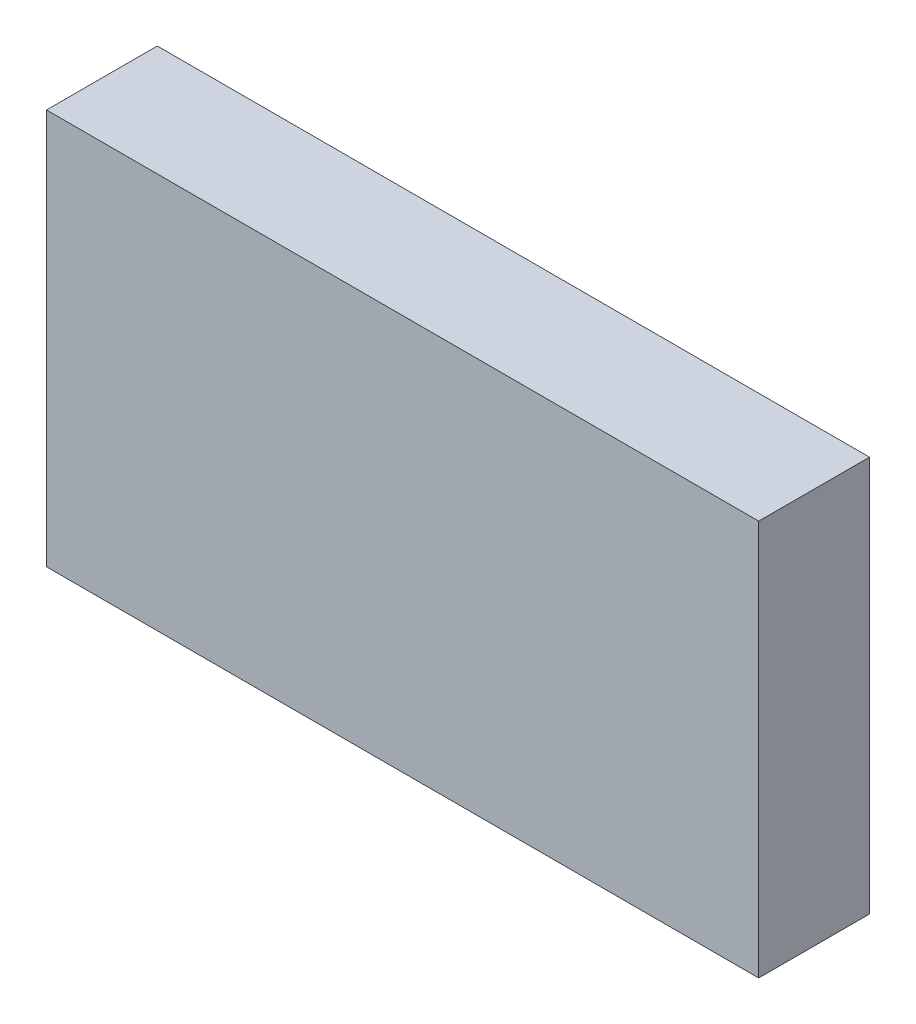
SolidWorks part; units mm, degrees
material "Pine"
ref_plane "Front Plane" through (0, 0, 0) normal (0, 0, 1) x (1, 0, 0)
ref_plane "Top Plane" through (0, 0, 0) normal (0, 1, 0) x (1, 0, 0)
ref_plane "Right Plane" through (0, 0, 0) normal (1, 0, 0) x (0, 0, -1)
sketch "Sketch1" plane through (0, 0, 0) normal (0, 0, 1) x (1, 0, 0)
  line L0 (8932.6508, -5243.5125) -> (10226.1458, -5243.5125)
  line L1 (9086.3208, -4722.0918) -> (10222.9708, -4853.7812)
  line L2 (8914.8708, -6342.0625) -> (10197.5708, -6342.0625)
  line L3 (8914.8708, -5808.6625) -> (10197.5708, -5808.6625)
  line L4 (8919.6333, -5253.0375) -> (10218.2083, -5253.0375)
  line L5 (9134.2633, -4656.1375) -> (9134.2633, -4638.3575)
  line L6 (9091.0833, -4638.3575) -> (9134.2633, -4638.3575)
  line L7 (9091.0833, -4567.2375) -> (9091.0833, -4638.3575)
  line L8 (9134.2633, -4656.1375) -> (9581.3033, -4656.1375)
  line L9 (9091.0833, -4567.2375) -> (9624.4833, -4567.2375)
  line L10 (9581.3033, -4656.1375) -> (9581.3033, -4638.3575)
  line L11 (9581.3033, -4638.3575) -> (9624.4833, -4638.3575)
  line L12 (9624.4833, -4567.2375) -> (9624.4833, -4638.3575)
  line L13 (8932.6508, -5225.7325) -> (9344.9775, -5225.7325)
  line L14 (8932.6508, -5256.2125) -> (8932.6508, -5243.5125)
  line L15 (8911.6958, -5256.2125) -> (8932.6508, -5256.2125)
  line L16 (8914.8708, -4722.0918) -> (9086.3208, -4722.0918)
  line L17 (8911.6958, -4715.5913) -> (8932.6508, -4715.5913)
  line L18 (8914.8708, -6342.0625) -> (8914.8708, -5808.6625)
  line L19 (12082.9917, -4722.0918) -> (10946.3417, -4853.7812)
  line L20 (12236.6617, -5243.5125) -> (10943.1667, -5243.5125)
  line L21 (10951.1042, -5253.0375) -> (12249.6792, -5253.0375)
  line L22 (10838.3917, -5656.2625) -> (11308.2917, -5656.2625)
  line L23 (10838.3917, -5719.7625) -> (11308.2917, -5719.7625)
  line L24 (10838.3917, -5742.5368) -> (11308.2917, -5742.5368)
  line L25 (10806.6417, -6342.0625) -> (11340.0417, -6342.0625)
  line L26 (10803.4667, -6335.7125) -> (11343.2167, -6335.7125)
  line L27 (10803.4667, -6317.9325) -> (11343.2167, -6317.9325)
  line L28 (10943.1667, -5225.7325) -> (11376.4483, -5225.7325)
  line L29 (11506.7292, -4754.5625) -> (10806.6417, -4827.5875)
  line L30 (11506.7292, -4567.2375) -> (11506.7292, -4754.5625)
  line L31 (10806.6417, -4567.2375) -> (10806.6417, -4827.5875)
  line L32 (10806.6417, -4567.2375) -> (11506.7292, -4567.2375)
  line L33 (10235.6708, -6329.3625) -> (10245.1958, -6329.3625)
  line L34 (10245.1958, -6329.3625) -> (10254.7208, -6278.5625)
  line L35 (10302.3458, -6329.3625) -> (10311.8708, -6278.5625)
  line L36 (10302.3458, -6329.3625) -> (10292.8208, -6329.3625)
  line L37 (10245.1958, -5821.3625) -> (10254.7208, -5872.1625)
  line L38 (10235.6708, -5821.3625) -> (10245.1958, -5821.3625)
  line L39 (10292.8208, -5821.3625) -> (10302.3458, -5821.3625)
  line L40 (10302.3458, -5821.3625) -> (10311.8708, -5872.1625)
  line L41 (10235.6708, -5821.3625) -> (10235.6708, -6329.3625)
  line L42 (10254.7208, -5872.1625) -> (10254.7208, -6278.5625)
  line L43 (10311.8708, -5872.1625) -> (10311.8708, -6278.5625)
  line L44 (10292.8208, -5821.3625) -> (10292.8208, -6329.3625)
  line L45 (8932.6508, -5225.7325) -> (8932.6508, -4715.5913)
  line L46 (8911.6958, -4715.5913) -> (8911.6958, -5256.2125)
  line L47 (8914.8708, -5248.275) -> (8914.8708, -4722.0918)
  line L48 (8919.6333, -5253.0375) -> (8914.8708, -5248.275)
  line L49 (8914.8708, -5145.0875) -> (8937.426, -5145.0875)
  line L50 (8914.8708, -5202.2375) -> (8937.426, -5202.2375)
  line L51 (10838.3917, -5656.2625) -> (10838.3917, -5719.7625)
  line L52 (10832.0417, -5736.1868) -> (10856.1717, -5736.1868)
  line L53 (10806.6417, -6342.0625) -> (10806.6417, -5818.7368)
  line L54 (10832.0417, -5649.9125) -> (10856.1717, -5649.9125)
  line L55 (10832.0417, -5726.1125) -> (10856.1717, -5726.1125)
  line L56 (10806.6417, -5818.7368) -> (10833.9015, -5818.7368)
  line L57 (10832.0417, -5806.0442) -> (10851.6815, -5806.0442)
  line L58 (10856.1717, -5801.5541) -> (10856.1717, -5736.1868)
  line L59 (10838.3917, -5814.2467) -> (10838.3917, -5742.5368)
  line L60 (10832.0417, -5806.0442) -> (10832.0417, -5736.1868)
  line L61 (10803.4667, -6317.9325) -> (10803.4667, -6335.7125)
  line L62 (10197.5708, -5808.6625) -> (10197.5708, -6342.0625)
  line L63 (9762.3842, -6348.4125) -> (9762.3842, -5802.3125)
  line L64 (9780.1642, -6348.4125) -> (9762.3842, -6348.4125)
  line L65 (9780.1642, -5802.3125) -> (9780.1642, -6348.4125)
  line L66 (9762.3842, -5802.3125) -> (9780.1642, -5802.3125)
  line L67 (9332.2775, -6348.4125) -> (9332.2775, -5802.3125)
  line L68 (9332.2775, -6348.4125) -> (9350.0575, -6348.4125)
  line L69 (9350.0575, -5802.3125) -> (9350.0575, -6348.4125)
  line L70 (9332.2775, -5802.3125) -> (9350.0575, -5802.3125)
  line L71 (9993.8374, -6061.075) -> (9993.8374, -6045.2418)
  line L72 (9998.5999, -6065.8375) -> (10014.4331, -6065.8375)
  line L73 (9998.5999, -6084.8875) -> (10014.4331, -6084.8875)
  line L74 (9993.8374, -6105.4832) -> (9993.8374, -6089.65)
  line L75 (9974.7874, -6105.4832) -> (9974.7874, -6089.65)
  line L76 (9954.1917, -6084.8875) -> (9970.0249, -6084.8875)
  line L77 (9974.7874, -6061.075) -> (9974.7874, -6045.2418)
  line L78 (9954.1917, -6065.8375) -> (9970.0249, -6065.8375)
  line L79 (10793.9417, -6237.2875) -> (10816.4969, -6237.2875)
  line L80 (10793.9417, -6294.4375) -> (10816.4969, -6294.4375)
  line L81 (10856.1717, -5649.9125) -> (10856.1717, -5726.1125)
  line L82 (10832.0417, -5726.1125) -> (10832.0417, -5649.9125)
  line L83 (10226.1458, -5225.7325) -> (10226.1458, -5243.5125)
  line L84 (10205.1908, -5257.8) -> (10205.1908, -4844.2499)
  line L85 (10230.9083, -4844.2499) -> (10230.9083, -5257.8)
  line L86 (10205.1908, -5257.8) -> (10230.9083, -5257.8)
  line L87 (10205.1908, -4844.2499) -> (10230.9083, -4844.2499)
  line L88 (10946.3417, -5176.8375) -> (10968.8969, -5176.8375)
  line L89 (9349.4676, -5141.9125) -> (9358.2674, -5141.9125)
  line L90 (10946.3417, -5119.6875) -> (10968.8969, -5119.6875)
  line L91 (9929.011, -4660.9635) -> (10066.0807, -4660.9635)
  line L92 (9929.011, -4678.7435) -> (10066.0807, -4678.7435)
  line L93 (10943.1667, -5225.7325) -> (10943.1667, -5243.5125)
  line L94 (10946.3417, -5248.275) -> (10951.1042, -5253.0375)
  line L95 (10946.3417, -5257.8063) -> (10946.3417, -4849.0188)
  line L96 (10964.1217, -5257.8) -> (10964.1217, -4844.2499)
  line L97 (10938.4042, -4844.2499) -> (10938.4042, -5257.8)
  line L98 (10938.4042, -5257.8) -> (10964.1217, -5257.8)
  line L99 (10964.1217, -4844.2499) -> (10938.4042, -4844.2499)
  line L100 (10344.8908, -4560.8875) -> (10369.0208, -4560.8875)
  line L101 (10344.8908, -4560.8875) -> (10369.0208, -4560.8875)
  line L102 (10800.2917, -4560.8875) -> (10824.4217, -4560.8875)
  line L103 (10200.4156, -5119.6875) -> (10222.9708, -5119.6875)
  line L104 (10200.4156, -5176.8375) -> (10222.9708, -5176.8375)
  line L105 (9344.9775, -5146.4026) -> (9344.9775, -5225.7325)
  line L106 (10344.8908, -4560.8875) -> (10344.8908, -4833.9375)
  line L107 (9792.8642, -5225.7325) -> (9792.8642, -5146.4026)
  line L108 (9362.7575, -5225.7325) -> (9775.0842, -5225.7325)
  line L109 (9680.3633, -4761.8396) -> (9680.3633, -4559.9604)
  line L110 (9656.2333, -4559.9604) -> (9680.3633, -4559.9604)
  line L111 (9656.2333, -4761.8396) -> (9680.3633, -4761.8396)
  line L112 (9656.2333, -4761.8396) -> (9656.2333, -4559.9604)
  line L113 (9779.5743, -5141.9125) -> (9788.374, -5141.9125)
  line L114 (10070.5708, -4665.4536) -> (10070.5708, -4674.2534)
  line L115 (9924.5208, -4674.2534) -> (9924.5208, -4665.4536)
  line L116 (12127.4417, -6188.3925) -> (12205.5015, -6188.3925)
  line L117 (12209.9917, -6170.6125) -> (12209.9917, -6183.9024)
  line L118 (9792.8642, -5225.7325) -> (10226.1458, -5225.7325)
  line L119 (9662.5833, -4754.5625) -> (10362.6708, -4827.5875)
  line L120 (9662.5833, -4567.2375) -> (9662.5833, -4754.5625)
  line L121 (10362.6708, -4567.2375) -> (10362.6708, -4827.5875)
  line L122 (9662.5833, -4567.2375) -> (10362.6708, -4567.2375)
  line L123 (10824.4217, -4833.9375) -> (10800.2917, -4833.9375)
  line L124 (10800.2917, -4833.9375) -> (10800.2917, -4560.8875)
  line L125 (10824.4217, -4560.8875) -> (10824.4217, -4833.9375)
  line L126 (10344.8908, -4833.9375) -> (10369.0208, -4833.9375)
  line L127 (10369.0208, -4833.9375) -> (10369.0208, -4560.8875)
  line L128 (10222.9708, -5248.275) -> (10218.2083, -5253.0375)
  line L129 (10222.9708, -5257.8063) -> (10222.9708, -4849.0188)
  line L130 (11734.6544, -5701.375) -> (11739.2301, -5701.375)
  line L131 (9362.7575, -5225.7325) -> (9362.7575, -5146.4026)
  line L132 (9775.0842, -5146.4026) -> (9775.0842, -5225.7325)
  line L133 (11761.3864, -5701.375) -> (11756.8282, -5701.375)
  line L134 (11734.6544, -5693.755) -> (11739.2301, -5693.755)
  line L135 (11761.4039, -5693.755) -> (11756.8282, -5693.755)
  line L136 (11734.6544, -5701.375) -> (11739.2301, -5701.375)
  line L137 (11744.3462, -5721.3024) -> (11744.3462, -5706.4179)
  line L138 (11751.7122, -5721.3024) -> (11751.7122, -5706.4179)
  line L139 (11740.0917, -6170.6125) -> (11740.0917, -6183.9024)
  line L140 (11689.2917, -6188.3925) -> (11822.6417, -6188.3925)
  line L141 (11689.2917, -6348.4093) -> (11689.2917, -6164.2657)
  line L142 (11689.2917, -6164.2657) -> (11746.4417, -6164.2657)
  line L143 (11746.4417, -6164.2657) -> (11746.4417, -6188.3925)
  line L144 (11689.2917, -6164.2657) -> (11746.4417, -6164.2657)
  line L145 (11340.0417, -5818.7368) -> (11340.0417, -6342.0625)
  line L146 (11290.5117, -5726.1125) -> (11314.6417, -5726.1125)
  line L147 (11290.5117, -5649.9125) -> (11290.5117, -5726.1125)
  line L148 (11340.0417, -5818.7368) -> (11312.7818, -5818.7368)
  line L149 (11314.6417, -5806.0442) -> (11295.0018, -5806.0442)
  line L150 (11290.5117, -5801.5541) -> (11290.5117, -5736.1868)
  line L151 (11308.2917, -5814.2467) -> (11308.2917, -5742.5368)
  line L152 (11314.6417, -5806.0442) -> (11314.6417, -5736.1868)
  line L153 (11290.5117, -5736.1868) -> (11314.6417, -5736.1868)
  line L154 (11848.0417, -6267.1325) -> (11962.3417, -6267.1325)
  line L155 (11962.3417, -6267.1325) -> (11962.3417, -6203.6325)
  line L156 (11343.2167, -6317.9325) -> (11343.2167, -6335.7125)
  line L157 (11365.4417, -5656.2625) -> (11365.4417, -5719.7625)
  line L158 (11365.4417, -5656.2625) -> (11479.7417, -5656.2625)
  line L159 (11778.1917, -6071.3937) -> (11802.3217, -6071.3937)
  line L160 (11314.6417, -5726.1125) -> (11314.6417, -5649.9125)
  line L161 (11314.6417, -5649.9125) -> (11290.5117, -5649.9125)
  line L162 (11308.2917, -5719.7625) -> (11308.2917, -5656.2625)
  line L163 (11689.2917, -6348.4093) -> (11713.4217, -6348.4093)
  line L164 (12203.6417, -6164.2657) -> (12260.7917, -6164.2657)
  line L165 (11713.4217, -6348.4093) -> (11713.4217, -6164.2657)
  line L166 (11695.6417, -6342.0625) -> (11695.6417, -6170.6125)
  line L167 (11695.6417, -6048.5337) -> (11699.4517, -6052.3437)
  line L168 (11822.6417, -6292.5325) -> (11822.6417, -6188.3925)
  line L169 (11695.6417, -6342.0625) -> (11695.6417, -6170.6125)
  line L170 (11848.0417, -6203.6325) -> (11962.3417, -6203.6325)
  line L171 (11848.0417, -6203.6325) -> (11848.0417, -6267.1325)
  line L172 (11987.7417, -6267.1325) -> (11987.7417, -6203.6325)
  line L173 (11784.5417, -6077.7437) -> (11784.5417, -6141.2438)
  line L174 (11517.8417, -5656.2625) -> (11632.1417, -5656.2625)
  line L175 (11632.1417, -5656.2625) -> (11632.1417, -5719.7625)
  line L176 (11632.1417, -5719.7625) -> (11517.8417, -5719.7625)
  line L177 (11517.8417, -5719.7625) -> (11517.8417, -5656.2625)
  line L178 (11692.4667, -6028.2137) -> (11692.4667, -6045.9937)
  line L179 (11695.6417, -5979.3188) -> (11718.1969, -5979.3188)
  line L180 (11695.6417, -5922.1687) -> (11718.1969, -5922.1687)
  line L181 (11821.0415, -5722.9375) -> (11821.0415, -5943.6)
  line L182 (11687.7042, -5651.5) -> (11701.9917, -5651.5)
  line L183 (11687.7042, -5651.5) -> (11687.7042, -6055.5251)
  line L184 (11687.7042, -6055.5251) -> (11701.9917, -6055.5251)
  line L185 (11701.9917, -6055.5251) -> (11701.9917, -5651.5)
  line L186 (11695.6417, -6055.2013) -> (11695.6417, -5649.595)
  line L187 (11695.6417, -5656.2625) -> (11695.6417, -6048.5337)
  line L188 (11695.6417, -6170.6125) -> (11740.0917, -6170.6125)
  line L189 (12203.6417, -6164.2657) -> (12203.6417, -6188.3925)
  line L190 (12254.4417, -6342.0625) -> (12254.4417, -6170.6125)
  line L191 (12129.0419, -5943.6) -> (12129.0419, -5722.9375)
  line L192 (12254.4417, -6048.5337) -> (12250.6317, -6052.3437)
  line L193 (12257.6167, -6045.9937) -> (12257.6167, -6028.2137)
  line L194 (12248.0917, -5651.5) -> (12262.3792, -5651.5)
  line L195 (12262.3792, -5651.5) -> (12262.3792, -6055.5251)
  line L196 (12262.3792, -6055.5251) -> (12248.0917, -6055.5251)
  line L197 (12248.0917, -6055.5251) -> (12248.0917, -5651.5)
  line L198 (12254.4417, -6141.2438) -> (12254.4417, -6077.7437)
  line L199 (12236.6617, -6164.2657) -> (12260.7917, -6164.2657)
  line L200 (12102.0417, -6267.1325) -> (11987.7417, -6267.1325)
  line L201 (11330.1865, -6237.2875) -> (11352.7417, -6237.2875)
  line L202 (11330.1865, -6294.4375) -> (11352.7417, -6294.4375)
  line L203 (11474.6617, -5851.8425) -> (11492.4417, -5851.8425)
  line L204 (11474.6617, -5808.6625) -> (11474.6617, -5851.8425)
  line L205 (11403.5417, -5808.6625) -> (11474.6617, -5808.6625)
  line L206 (11492.4417, -5851.8425) -> (11492.4417, -6298.8825)
  line L207 (11403.5417, -6342.0625) -> (11403.5417, -5808.6625)
  line L208 (11474.6617, -6298.8825) -> (11492.4417, -6298.8825)
  line L209 (11474.6617, -6342.0625) -> (11474.6617, -6298.8825)
  line L210 (11403.5417, -6342.0625) -> (11474.6617, -6342.0625)
  line L211 (11619.4417, -5851.8425) -> (11601.6617, -5851.8425)
  line L212 (11601.6617, -5808.6625) -> (11601.6617, -5851.8425)
  line L213 (11530.5417, -5808.6625) -> (11601.6617, -5808.6625)
  line L214 (11619.4417, -5851.8425) -> (11619.4417, -6298.8825)
  line L215 (11530.5417, -6342.0625) -> (11530.5417, -5808.6625)
  line L216 (11619.4417, -6298.8825) -> (11601.6617, -6298.8825)
  line L217 (11601.6617, -6342.0625) -> (11601.6617, -6298.8825)
  line L218 (11530.5417, -6342.0625) -> (11601.6617, -6342.0625)
  line L219 (11479.7417, -5719.7625) -> (11479.7417, -5656.2625)
  line L220 (11365.4417, -5719.7625) -> (11479.7417, -5719.7625)
  line L221 (11778.1917, -6147.5937) -> (11802.3217, -6147.5937)
  line L222 (11802.3217, -6071.3937) -> (11802.3217, -6147.5937)
  line L223 (11778.1917, -6147.5937) -> (11778.1917, -6071.3937)
  line L224 (12254.4417, -5922.1687) -> (12231.8865, -5922.1687)
  line L225 (12254.4417, -5979.3188) -> (12231.8865, -5979.3188)
  line L226 (12254.4417, -6055.2013) -> (12254.4417, -5649.595)
  line L227 (12254.4417, -6048.5337) -> (12254.4417, -5656.2625)
  line L228 (11841.6917, -5702.2873) -> (12108.3917, -5702.2873)
  line L229 (11822.6417, -6292.5325) -> (12127.4417, -6292.5325)
  line L230 (12127.4417, -6292.5325) -> (12127.4417, -6188.3925)
  line L231 (12254.4417, -6170.6125) -> (12209.9917, -6170.6125)
  line L232 (11695.6417, -6342.0625) -> (12254.4417, -6342.0625)
  line L233 (12236.6617, -6348.4093) -> (12260.7917, -6348.4093)
  line L234 (12260.7917, -6348.4093) -> (12260.7917, -6164.2657)
  line L235 (12236.6617, -6348.4093) -> (12236.6617, -6164.2657)
  line L236 (12102.0417, -6203.6325) -> (12102.0417, -6267.1325)
  line L237 (11987.7417, -6203.6325) -> (12102.0417, -6203.6325)
  line L238 (12236.6617, -6147.5937) -> (12236.6617, -6071.3937)
  line L239 (12203.6417, -6188.3925) -> (12260.7917, -6188.3925)
  line L240 (11098.7417, -4665.4536) -> (11098.7417, -4674.2534)
  line L241 (11394.2283, -5146.4026) -> (11394.2283, -5225.7325)
  line L242 (11376.4483, -5225.7325) -> (11376.4483, -5146.4026)
  line L243 (11394.2283, -5225.7325) -> (11806.555, -5225.7325)
  line L244 (11841.6917, -5964.2502) -> (12108.3917, -5964.2502)
  line L245 (12236.6617, -6147.5937) -> (12260.7917, -6147.5937)
  line L246 (12236.6617, -5256.2125) -> (12236.6617, -5243.5125)
  line L247 (12260.7917, -6147.5937) -> (12260.7917, -6071.3937)
  line L248 (12260.7917, -6071.3937) -> (12236.6617, -6071.3937)
  line L249 (12254.4417, -6077.7437) -> (11784.5417, -6077.7437)
  line L250 (11784.5417, -6141.2438) -> (12254.4417, -6141.2438)
  line L252 (12254.4417, -5656.2625) -> (11695.6417, -5656.2625)
  line L253 (11699.4517, -6052.3437) -> (12250.6317, -6052.3437)
  line L254 (11692.4667, -6045.9937) -> (12257.6167, -6045.9937)
  line L255 (11692.4667, -6028.2137) -> (12257.6167, -6028.2137)
  line L256 (11824.335, -5146.4026) -> (11824.335, -5225.7325)
  line L257 (11811.0451, -5141.9125) -> (11819.8449, -5141.9125)
  line L258 (11244.7917, -4674.2534) -> (11244.7917, -4665.4536)
  line L259 (11806.555, -5225.7325) -> (11806.555, -5146.4026)
  line L260 (11488.9492, -4761.8396) -> (11488.9492, -4559.9604)
  line L261 (11488.9492, -4559.9604) -> (11513.0792, -4559.9604)
  line L262 (11488.9492, -4761.8396) -> (11513.0792, -4761.8396)
  line L263 (11513.0792, -4761.8396) -> (11513.0792, -4559.9604)
  line L264 (11240.3015, -4660.9635) -> (11103.2318, -4660.9635)
  line L265 (11103.2318, -4678.7435) -> (11240.3015, -4678.7435)
  line L266 (12236.6617, -5225.7325) -> (12236.6617, -4715.5913)
  line L267 (12257.6167, -4715.5913) -> (12257.6167, -5256.2125)
  line L268 (12254.4417, -5248.275) -> (12254.4417, -4722.0918)
  line L269 (12236.6617, -5225.7325) -> (11824.335, -5225.7325)
  line L270 (12035.0492, -4656.1375) -> (12035.0492, -4638.3575)
  line L271 (12078.2292, -4638.3575) -> (12035.0492, -4638.3575)
  line L272 (12078.2292, -4567.2375) -> (12078.2292, -4638.3575)
  line L273 (12035.0492, -4656.1375) -> (11588.0092, -4656.1375)
  line L274 (11544.8292, -4567.2375) -> (12078.2292, -4567.2375)
  line L275 (11588.0092, -4656.1375) -> (11588.0092, -4638.3575)
  line L276 (11544.8292, -4638.3575) -> (11588.0092, -4638.3575)
  line L277 (11544.8292, -4567.2375) -> (11544.8292, -4638.3575)
  line L278 (12249.6792, -5253.0375) -> (12254.4417, -5248.275)
  line L280 (12257.6167, -5256.2125) -> (12236.6617, -5256.2125)
  line L281 (12231.8865, -5145.0875) -> (12254.4417, -5145.0875)
  line L282 (12231.8865, -5202.2375) -> (12254.4417, -5202.2375)
  line L283 (12236.6617, -4715.5913) -> (12257.6167, -4715.5913)
  line L284 (12082.9917, -4722.0918) -> (12254.4417, -4722.0918)
  line L285 (11380.9385, -5141.9125) -> (11389.7382, -5141.9125)
  circle A0 centre (8923.7608, -4778.9042) radius 1.5875
  circle A1 centre (9062.6598, -4736.3765) radius 2.3685
  circle A2 centre (9051.3958, -6281.7375) radius 22.225
  circle A3 centre (9083.1458, -6249.9875) radius 1.5875
  circle A4 centre (9083.1458, -6313.4875) radius 1.5875
  circle A5 centre (9019.6458, -6249.9875) radius 1.5875
  circle A6 centre (9019.6458, -6313.4875) radius 1.5875
  circle A7 centre (8972.3383, -5202.2375) radius 1.5875
  circle A8 centre (8923.7608, -5015.9708) radius 1.5875
  circle A9 centre (8923.7608, -5134.5042) radius 1.5875
  circle A10 centre (9054.5708, -5234.6225) radius 1.5875
  circle A11 centre (8923.7608, -4897.4375) radius 1.5875
  circle A12 centre (8972.3383, -5087.9375) radius 1.5875
  circle A13 centre (8972.3383, -5145.0875) radius 1.5875
  circle A14 centre (10847.2817, -5668.9625) radius 1.5875
  circle A15 centre (10847.2817, -5707.0625) radius 1.5875
  circle A16 centre (10847.2817, -5755.2368) radius 1.5875
  circle A17 centre (10851.4092, -6237.2875) radius 1.5875
  circle A18 centre (10851.4092, -6294.4375) radius 1.5875
  circle A19 centre (10847.2817, -5793.3442) radius 1.5875
  arc A20 (10833.9015, -5818.7368) -> (10838.3917, -5814.2467) centre (10836.1466, -5816.4918) ccw
  arc A21 (10851.6815, -5806.0442) -> (10856.1717, -5801.5541) centre (10853.9266, -5803.7992) ccw
  circle A22 centre (10882.8417, -6040.4375) radius 1.5875
  circle A23 centre (10882.8417, -6218.2375) radius 1.5875
  circle A24 centre (10882.8417, -5862.6375) radius 1.5875
  circle A25 centre (10908.2417, -6326.8225) radius 1.5875
  circle A26 centre (10908.2417, -6326.8225) radius 1.5875
  circle A27 centre (10851.4092, -6180.1375) radius 1.5875
  circle A28 centre (10815.5317, -4783.4231) radius 1.5875
  circle A29 centre (10815.5317, -4696.9488) radius 1.5875
  circle A30 centre (10815.5317, -4610.4746) radius 1.5875
  circle A31 centre (10979.1323, -4867.0082) radius 2.3685
  circle A32 centre (10190.1802, -4867.0082) radius 2.3685
  circle A33 centre (10955.2317, -4929.9812) radius 1.5875
  circle A34 centre (10955.2317, -5031.5812) radius 1.5875
  circle A35 centre (10214.0808, -4929.9812) radius 1.5875
  circle A36 centre (10214.0808, -5031.5812) radius 1.5875
  circle A37 centre (9341.1675, -6265.8625) radius 1.5875
  circle A38 centre (9771.2742, -5884.8625) radius 1.5875
  circle A39 centre (9771.2742, -6138.8625) radius 1.5875
  circle A40 centre (9771.2742, -6011.8625) radius 1.5875
  arc A41 (10036.2287, -6113.8083) -> (10051.3426, -6111.6033) centre (10042.9639, -6107.0732) ccw
  arc A42 (10051.3426, -6111.6033) -> (10051.3426, -6039.1217) centre (9984.3124, -6075.3625) ccw
  arc A43 (10051.3426, -6039.1217) -> (10036.2287, -6036.9167) centre (10042.9639, -6043.6518) ccw
  arc A44 (10034.5851, -6102.5431) -> (10034.5851, -6048.1819) centre (9984.3124, -6075.3625) ccw
  arc A45 (10034.5851, -6102.5431) -> (10036.2287, -6113.8083) centre (10042.9639, -6107.0732) ccw
  arc A46 (10036.2287, -6036.9167) -> (10034.5851, -6048.1819) centre (10042.9639, -6043.6518) ccw
  arc A47 (9945.8666, -6127.2787) -> (9948.0717, -6142.3927) centre (9952.6018, -6134.0139) ccw
  arc A48 (9948.0717, -6142.3927) -> (10020.5532, -6142.3927) centre (9984.3124, -6075.3625) ccw
  arc A49 (10020.5532, -6142.3927) -> (10022.7583, -6127.2787) centre (10016.0231, -6134.0139) ccw
  arc A50 (9957.1319, -6125.6352) -> (10011.493, -6125.6352) centre (9984.3124, -6075.3625) ccw
  arc A51 (9957.1319, -6125.6352) -> (9945.8666, -6127.2787) centre (9952.6018, -6134.0139) ccw
  arc A52 (10022.7583, -6127.2787) -> (10011.493, -6125.6352) centre (10016.0231, -6134.0139) ccw
  arc A53 (9932.3962, -6036.9167) -> (9917.2822, -6039.1217) centre (9925.661, -6043.6518) ccw
  arc A54 (9917.2822, -6039.1217) -> (9917.2822, -6111.6033) centre (9984.3124, -6075.3625) ccw
  arc A55 (9917.2822, -6111.6033) -> (9932.3962, -6113.8083) centre (9925.661, -6107.0732) ccw
  arc A56 (9934.0398, -6048.1819) -> (9934.0398, -6102.5431) centre (9984.3124, -6075.3625) ccw
  arc A57 (9934.0398, -6048.1819) -> (9932.3962, -6036.9167) centre (9925.661, -6043.6518) ccw
  arc A58 (9932.3962, -6113.8083) -> (9934.0398, -6102.5431) centre (9925.661, -6107.0732) ccw
  arc A59 (9945.8666, -6023.4463) -> (9957.1319, -6025.0898) centre (9952.6018, -6016.7111) ccw
  arc A60 (10011.493, -6025.0898) -> (10022.7583, -6023.4463) centre (10016.0231, -6016.7111) ccw
  arc A61 (10011.493, -6025.0898) -> (9957.1319, -6025.0898) centre (9984.3124, -6075.3625) ccw
  arc A62 (9948.0717, -6008.3323) -> (9945.8666, -6023.4463) centre (9952.6018, -6016.7111) ccw
  arc A63 (10020.5532, -6008.3323) -> (9948.0717, -6008.3323) centre (9984.3124, -6075.3625) ccw
  arc A64 (10022.7583, -6023.4463) -> (10020.5532, -6008.3323) centre (10016.0231, -6016.7111) ccw
  arc A65 (10005.0943, -6187.7574) -> (10096.7073, -6096.1443) centre (9984.3124, -6075.3625) ccw
  arc A66 (9993.8374, -6178.3911) -> (10005.0943, -6187.7574) centre (10003.3624, -6178.3911) ccw
  arc A67 (10001.6306, -6169.0249) -> (10077.9748, -6092.6807) centre (9984.3124, -6075.3625) ccw
  arc A68 (10087.3411, -6084.8875) -> (10077.9748, -6092.6807) centre (10087.3411, -6094.4125) ccw
  arc A69 (10001.6306, -6169.0249) -> (9993.8374, -6178.3911) centre (10003.3624, -6178.3911) ccw
  arc A70 (9963.5306, -6187.7574) -> (9974.7874, -6178.3911) centre (9965.2624, -6178.3911) ccw
  arc A71 (9871.9176, -6096.1443) -> (9963.5306, -6187.7574) centre (9984.3124, -6075.3625) ccw
  arc A72 (9881.2838, -6084.8875) -> (9871.9176, -6096.1443) centre (9881.2838, -6094.4125) ccw
  arc A73 (9890.65, -6092.6807) -> (9966.9943, -6169.0249) centre (9984.3124, -6075.3625) ccw
  arc A74 (9974.7874, -6178.3911) -> (9966.9943, -6169.0249) centre (9965.2624, -6178.3911) ccw
  arc A75 (9890.65, -6092.6807) -> (9881.2838, -6084.8875) centre (9881.2838, -6094.4125) ccw
  arc A76 (9871.9176, -6054.5807) -> (9881.2838, -6065.8375) centre (9881.2838, -6056.3125) ccw
  arc A77 (9963.5306, -5962.9676) -> (9871.9176, -6054.5807) centre (9984.3124, -6075.3625) ccw
  arc A78 (9974.7874, -5972.3339) -> (9963.5306, -5962.9676) centre (9965.2624, -5972.3339) ccw
  arc A79 (9966.9943, -5981.7001) -> (9890.65, -6058.0443) centre (9984.3124, -6075.3625) ccw
  arc A80 (9881.2838, -6065.8375) -> (9890.65, -6058.0443) centre (9881.2838, -6056.3125) ccw
  arc A81 (9966.9943, -5981.7001) -> (9974.7874, -5972.3339) centre (9965.2624, -5972.3339) ccw
  arc A82 (10077.9748, -6058.0443) -> (10087.3411, -6065.8375) centre (10087.3411, -6056.3125) ccw
  arc A83 (9993.8374, -5972.3339) -> (10001.6306, -5981.7001) centre (10003.3624, -5972.3339) ccw
  arc A84 (10077.9748, -6058.0443) -> (10001.6306, -5981.7001) centre (9984.3124, -6075.3625) ccw
  arc A85 (10087.3411, -6065.8375) -> (10096.7073, -6054.5807) centre (10087.3411, -6056.3125) ccw
  arc A86 (10096.7073, -6054.5807) -> (10005.0943, -5962.9676) centre (9984.3124, -6075.3625) ccw
  arc A87 (10005.0943, -5962.9676) -> (9993.8374, -5972.3339) centre (10003.3624, -5972.3339) ccw
  arc A88 (10014.4331, -6065.8375) -> (10018.7361, -6059.0339) centre (10014.4331, -6061.075) ccw
  arc A89 (10018.7361, -6059.0339) -> (10000.641, -6040.9388) centre (9984.3124, -6075.3625) ccw
  arc A90 (10000.641, -6040.9388) -> (9993.8374, -6045.2418) centre (9998.5999, -6045.2418) ccw
  arc A91 (9993.8374, -6061.075) -> (9998.5999, -6065.8375) centre (9998.5999, -6061.075) ccw
  arc A92 (9993.8374, -6105.4832) -> (10000.641, -6109.7862) centre (9998.5999, -6105.4832) ccw
  arc A93 (10000.641, -6109.7862) -> (10018.7361, -6091.6911) centre (9984.3124, -6075.3625) ccw
  arc A94 (10018.7361, -6091.6911) -> (10014.4331, -6084.8875) centre (10014.4331, -6089.65) ccw
  arc A95 (9998.5999, -6084.8875) -> (9993.8374, -6089.65) centre (9998.5999, -6089.65) ccw
  arc A96 (9954.1917, -6084.8875) -> (9949.8888, -6091.6911) centre (9954.1917, -6089.65) ccw
  arc A97 (9949.8888, -6091.6911) -> (9967.9839, -6109.7862) centre (9984.3124, -6075.3625) ccw
  arc A98 (9967.9839, -6109.7862) -> (9974.7874, -6105.4832) centre (9970.0249, -6105.4832) ccw
  arc A99 (9974.7874, -6089.65) -> (9970.0249, -6084.8875) centre (9970.0249, -6089.65) ccw
  arc A100 (9970.0249, -6065.8375) -> (9974.7874, -6061.075) centre (9970.0249, -6061.075) ccw
  arc A101 (9949.8888, -6059.0339) -> (9954.1917, -6065.8375) centre (9954.1917, -6061.075) ccw
  arc A102 (9967.9839, -6040.9388) -> (9949.8888, -6059.0339) centre (9984.3124, -6075.3625) ccw
  arc A103 (9974.7874, -6045.2418) -> (9967.9839, -6040.9388) centre (9970.0249, -6045.2418) ccw
  arc A104 (10096.7073, -6096.1443) -> (10087.3411, -6084.8875) centre (10087.3411, -6094.4125) ccw
  circle A105 centre (9771.2742, -6265.8625) radius 1.5875
  circle A106 centre (9341.1675, -5884.8625) radius 1.5875
  circle A107 centre (9341.1675, -6138.8625) radius 1.5875
  circle A108 centre (9341.1675, -6011.8625) radius 1.5875
  circle A109 centre (11037.2315, -4887.5494) radius 15.0812
  arc A110 (9349.4676, -5141.9125) -> (9344.9775, -5146.4026) centre (9347.2226, -5144.1576) ccw
  arc A111 (9362.7575, -5146.4026) -> (9358.2674, -5141.9125) centre (9360.5124, -5144.1576) ccw
  circle A112 centre (9946.7458, -4669.8535) radius 1.5875
  arc A113 (9924.5208, -4674.2534) -> (9929.011, -4678.7435) centre (9926.7659, -4676.4984) ccw
  circle A114 centre (11003.8092, -5176.8375) radius 1.5875
  circle A115 centre (11003.8092, -5119.6875) radius 1.5875
  circle A116 centre (10353.7808, -4696.9488) radius 1.5875
  circle A117 centre (10353.7808, -4610.4746) radius 1.5875
  circle A118 centre (10353.7808, -4783.4231) radius 1.5875
  circle A119 centre (11003.8092, -5062.5375) radius 1.5875
  circle A120 centre (9353.8675, -5160.9625) radius 1.5875
  circle A121 centre (9638.7708, -5234.6225) radius 1.5875
  circle A122 centre (9671.4733, -4724.1144) radius 1.5875
  circle A123 centre (9671.4733, -4661.3637) radius 1.5875
  circle A124 centre (9671.4733, -4598.6129) radius 1.5875
  arc A125 (9792.8642, -5146.4026) -> (9788.374, -5141.9125) centre (9790.6191, -5144.1576) ccw
  arc A126 (9779.5743, -5141.9125) -> (9775.0842, -5146.4026) centre (9777.3292, -5144.1576) ccw
  circle A127 centre (10048.3458, -4669.8535) radius 1.5875
  arc A128 (10070.5708, -4665.4536) -> (10066.0807, -4660.9635) centre (10068.3258, -4663.2086) ccw
  arc A129 (10066.0807, -4678.7435) -> (10070.5708, -4674.2534) centre (10068.3258, -4676.4984) ccw
  circle A130 centre (9997.5458, -4669.8535) radius 1.5875
  arc A131 (9929.011, -4660.9635) -> (9924.5208, -4665.4536) centre (9926.7659, -4663.2086) ccw
  circle A132 centre (10132.081, -4887.5494) radius 15.0812
  circle A133 centre (10165.5033, -5176.8375) radius 1.5875
  circle A134 centre (10165.5033, -5119.6875) radius 1.5875
  circle A135 centre (9486.3708, -5234.6225) radius 1.5875
  circle A136 centre (10165.5033, -5062.5375) radius 1.5875
  circle A137 centre (9206.9708, -5234.6225) radius 1.5875
  circle A138 centre (10070.5708, -5234.6225) radius 1.5875
  circle A139 centre (9918.1708, -5234.6225) radius 1.5875
  circle A140 centre (9783.9742, -5160.9625) radius 1.5875
  circle A141 centre (9783.9742, -5193.9825) radius 1.5875
  circle A142 centre (9353.8675, -5193.9825) radius 1.5875
  circle A143 centre (11073.3417, -6326.8225) radius 1.5875
  circle A144 centre (11073.3417, -6326.8225) radius 1.5875
  circle A145 centre (11295.2742, -6180.1375) radius 1.5875
  circle A146 centre (11295.2742, -6294.4375) radius 1.5875
  circle A147 centre (11295.2742, -6237.2875) radius 1.5875
  circle A148 centre (11975.0417, -5692.775) radius 3.4925
  circle A149 centre (11263.8417, -5862.6375) radius 1.5875
  arc A150 (11739.2301, -5701.375) -> (11744.3462, -5706.4179) centre (11748.0292, -5697.565) ccw
  arc A151 (11751.7122, -5706.4179) -> (11756.8282, -5701.375) centre (11748.0292, -5697.565) ccw
  arc A152 (11744.3462, -5721.3024) -> (11751.7122, -5721.3024) centre (11748.0292, -5725.505) ccw
  arc A153 (11734.6544, -5693.755) -> (11724.9787, -5697.565) centre (11730.5667, -5697.565) ccw
  arc A154 (11756.8282, -5693.755) -> (11739.2301, -5693.755) centre (11748.0292, -5697.565) ccw
  arc A155 (11724.9787, -5697.565) -> (11734.6544, -5701.375) centre (11730.5667, -5697.565) ccw
  arc A156 (11761.3864, -5701.375) -> (11771.0797, -5697.565) centre (11765.4842, -5697.565) ccw
  arc A157 (11771.0797, -5697.565) -> (11761.4039, -5693.755) centre (11765.4917, -5697.565) ccw
  arc A158 (11740.0917, -6183.9024) -> (11744.5818, -6188.3925) centre (11742.3367, -6186.1474) ccw
  arc A159 (12205.5015, -6188.3925) -> (12209.9917, -6183.9024) centre (12207.7466, -6186.1474) ccw
  circle A160 centre (11299.4017, -5793.3442) radius 1.5875
  arc A161 (11308.2917, -5814.2467) -> (11312.7818, -5818.7368) centre (11310.5367, -5816.4918) ccw
  arc A162 (11290.5117, -5801.5541) -> (11295.0018, -5806.0442) centre (11292.7567, -5803.7992) ccw
  circle A163 centre (11704.5317, -6314.149) radius 1.5875
  circle A164 centre (11748.9817, -6208.7125) radius 1.5875
  circle A165 centre (11263.8417, -6218.2375) radius 1.5875
  circle A166 centre (11263.8417, -6040.4375) radius 1.5875
  circle A167 centre (11238.4417, -6326.8225) radius 1.5875
  circle A168 centre (11238.4417, -6326.8225) radius 1.5875
  circle A169 centre (11299.4017, -5668.9625) radius 1.5875
  circle A170 centre (11299.4017, -5707.0625) radius 1.5875
  circle A171 centre (11726.7567, -6179.5025) radius 1.5875
  circle A172 centre (11704.5317, -6199.3198) radius 1.5875
  circle A173 centre (11748.9817, -6272.2125) radius 1.5875
  circle A174 centre (11704.5317, -6256.7344) radius 1.5875
  circle A175 centre (11299.4017, -5755.2368) radius 1.5875
  circle A176 centre (11913.4467, -6301.4225) radius 1.5875
  circle A177 centre (11790.2567, -6301.4225) radius 1.5875
  circle A178 centre (11793.4317, -6128.5437) radius 1.5875
  circle A179 centre (11753.1092, -5865.0188) radius 1.5875
  circle A180 centre (11809.9417, -6037.1038) radius 1.5875
  circle A181 centre (11809.9417, -6037.1038) radius 1.5875
  circle A182 centre (11753.1092, -5922.1687) radius 1.5875
  circle A183 centre (11975.0417, -5973.7625) radius 3.4925
  circle A184 centre (11975.0417, -6037.1038) radius 1.5875
  circle A185 centre (11753.1092, -5979.3188) radius 1.5875
  circle A186 centre (11975.0417, -6037.1038) radius 1.5875
  arc A187 (11841.6917, -5702.2873) -> (11821.0415, -5722.9375) centre (11841.6917, -5722.9375) ccw
  circle A188 centre (11811.5292, -5833.2687) radius 3.4925
  arc A189 (11821.0415, -5943.6) -> (11841.6917, -5964.2502) centre (11841.6917, -5943.6) ccw
  circle A190 centre (12196.9742, -5865.0188) radius 1.5875
  arc A191 (12129.0419, -5722.9375) -> (12108.3917, -5702.2873) centre (12108.3917, -5722.9375) ccw
  circle A192 centre (12036.6367, -6301.4225) radius 1.5875
  circle A193 centre (12159.8267, -6301.4225) radius 1.5875
  circle A194 centre (12138.5542, -5833.2687) radius 3.4925
  circle A195 centre (12197.2917, -5761.0375) radius 15.0812
  circle A196 centre (11793.4317, -6090.4437) radius 1.5875
  circle A197 centre (12196.9742, -5922.1687) radius 1.5875
  arc A198 (12108.3917, -5964.2502) -> (12129.0419, -5943.6) centre (12108.3917, -5943.6) ccw
  circle A199 centre (12196.9742, -5979.3188) radius 1.5875
  circle A200 centre (12201.1017, -6272.2125) radius 1.5875
  circle A201 centre (12245.5517, -6314.149) radius 1.5875
  circle A202 centre (12245.5517, -6256.7344) radius 1.5875
  circle A203 centre (12201.1017, -6208.7125) radius 1.5875
  circle A204 centre (12223.3267, -6179.5025) radius 1.5875
  circle A205 centre (12245.5517, -6199.3198) radius 1.5875
  circle A206 centre (11171.7667, -4669.8535) radius 1.5875
  circle A207 centre (11222.5667, -4669.8535) radius 1.5875
  arc A208 (11240.3015, -4678.7435) -> (11244.7917, -4674.2534) centre (11242.5466, -4676.4984) ccw
  circle A209 centre (11385.3383, -5193.9825) radius 1.5875
  circle A210 centre (12106.6527, -4736.3765) radius 2.3685
  circle A211 centre (12140.1417, -6037.1038) radius 1.5875
  circle A212 centre (12140.1417, -6037.1038) radius 1.5875
  circle A213 centre (12245.5517, -6090.4437) radius 1.5875
  circle A214 centre (12245.5517, -6128.5437) radius 1.5875
  circle A215 centre (11385.3383, -5160.9625) radius 1.5875
  arc A216 (11824.335, -5146.4026) -> (11819.8449, -5141.9125) centre (11822.0899, -5144.1576) ccw
  arc A217 (11811.0451, -5141.9125) -> (11806.555, -5146.4026) centre (11808.8001, -5144.1576) ccw
  circle A218 centre (11815.445, -5193.9825) radius 1.5875
  circle A219 centre (11815.445, -5160.9625) radius 1.5875
  circle A220 centre (11530.5417, -5234.6225) radius 1.5875
  circle A221 centre (11962.3417, -5234.6225) radius 1.5875
  arc A222 (11244.7917, -4665.4536) -> (11240.3015, -4660.9635) centre (11242.5466, -4663.2086) ccw
  circle A223 centre (11682.9417, -5234.6225) radius 1.5875
  circle A224 centre (11497.8392, -4724.1144) radius 1.5875
  circle A225 centre (11497.8392, -4661.3637) radius 1.5875
  circle A226 centre (11497.8392, -4598.6129) radius 1.5875
  circle A227 centre (11120.9667, -4669.8535) radius 1.5875
  arc A228 (11103.2318, -4660.9635) -> (11098.7417, -4665.4536) centre (11100.9867, -4663.2086) ccw
  arc A229 (11098.7417, -4674.2534) -> (11103.2318, -4678.7435) centre (11100.9867, -4676.4984) ccw
  circle A230 centre (12196.9742, -5202.2375) radius 1.5875
  circle A231 centre (12245.5517, -5015.9708) radius 1.5875
  circle A232 centre (12245.5517, -5134.5042) radius 1.5875
  circle A233 centre (12114.7417, -5234.6225) radius 1.5875
  circle A234 centre (12245.5517, -4897.4375) radius 1.5875
  circle A235 centre (12245.5517, -4778.9042) radius 1.5875
  circle A236 centre (12196.9742, -5087.9375) radius 1.5875
  circle A237 centre (12196.9742, -5145.0875) radius 1.5875
  circle A238 centre (11098.7417, -5234.6225) radius 1.5875
  circle A239 centre (11251.1417, -5234.6225) radius 1.5875
  arc A240 (11380.9385, -5141.9125) -> (11376.4483, -5146.4026) centre (11378.6934, -5144.1576) ccw
  arc A241 (11394.2283, -5146.4026) -> (11389.7382, -5141.9125) centre (11391.9833, -5144.1576) ccw
sketch "PedOutline" plane through (0, 0, 0) normal (0, 0, 1) x (1, 0, 0)
  line L0 (11517.8417, -5656.2625) -> (11517.8417, -5719.7625)
  line L1 (11517.8417, -5719.7625) -> (11632.1417, -5719.7625)
  line L2 (11632.1417, -5719.7625) -> (11632.1417, -5656.2625)
  line L3 (11632.1417, -5656.2625) -> (11517.8417, -5656.2625)
  line L4 (11574.9917, -5719.7625) -> (11574.9917, -5656.2625) construction
  line L5 (11517.8417, -5688.0125) -> (11574.9917, -5688.0125) construction
  line L6 (11632.1417, -5688.0125) -> (11574.9917, -5688.0125) construction
  dimension "Ped_Width" = 114.3
  dimension "Ped_Height" = 63.5
extrude "PedOutline_Thickness" add sketch "PedOutline" against normal blind 17.78
